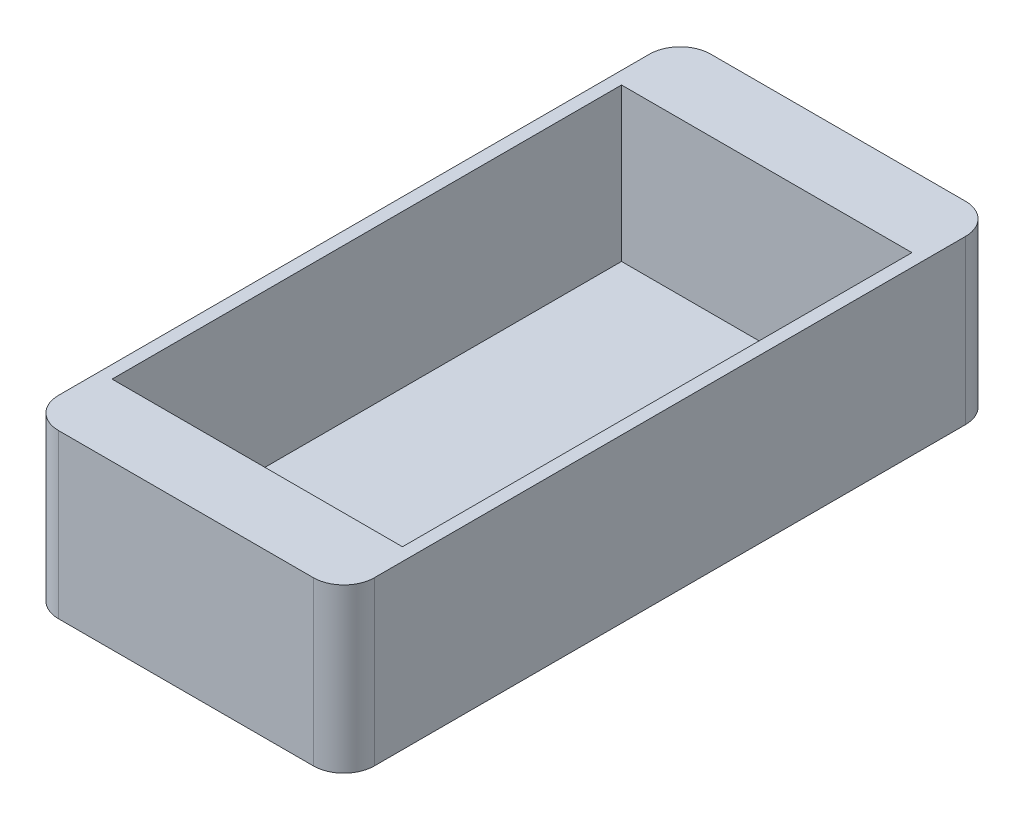
SolidWorks part; units mm, degrees
ref_plane "前视基准面" through (0, 0, 0) normal (0, 0, 1) x (1, 0, 0)
ref_plane "上视基准面" through (0, 0, 0) normal (0, 1, 0) x (1, 0, 0)
ref_plane "右视基准面" through (0, 0, 0) normal (1, 0, 0) x (0, 0, -1)
sketch "草图1" plane through (0, 0, 0) normal (0, 1, 0) x (1, 0, 0)
  line L1 (-14.25, 25) -> (14.25, 25)
  line L2 (-14.25, 25) -> (-14.25, -25)
  line L3 (-14.25, -25) -> (14.25, -25)
  line L4 (14.25, 25) -> (14.25, -25)
  line L5 (-14.25, 25) -> (14.25, -25) construction
  line L6 (-14.25, -25) -> (14.25, 25) construction
  line L7 (-15.5, 32) -> (15.5, 32)
  line L8 (-15.5, 32) -> (-15.5, -32)
  line L9 (-15.5, -32) -> (15.5, -32)
  line L10 (15.5, 32) -> (15.5, -32)
  line L11 (-15.5, 32) -> (15.5, -32) construction
  line L12 (-15.5, -32) -> (15.5, 32) construction
  point P0 (0, 0)
  point P6 (0, 0)
  dimension "D1" = 50
  dimension "D2" = 28.5
  dimension "D3" = 64
  dimension "D4" = 31
extrude "凸台-拉伸1" add sketch "草图1" along normal blind 15
sketch "草图2" plane through (0, 0, 0) normal (0, 1, 0) x (1, 0, 0)
  line L1 (-15.5, 32) -> (15.5, 32)
  line L2 (-15.5, 32) -> (-15.5, -32)
  line L3 (-15.5, -32) -> (15.5, -32)
  line L4 (15.5, 32) -> (15.5, -32)
extrude "凸台-拉伸2" add sketch "草图2" against normal blind 1
fillet "圆角1" radius 3 4 edges at (15.5, 7, 32) (-15.5, 7, 32) (15.5, 7, -32) (-15.5, 7, -32)
